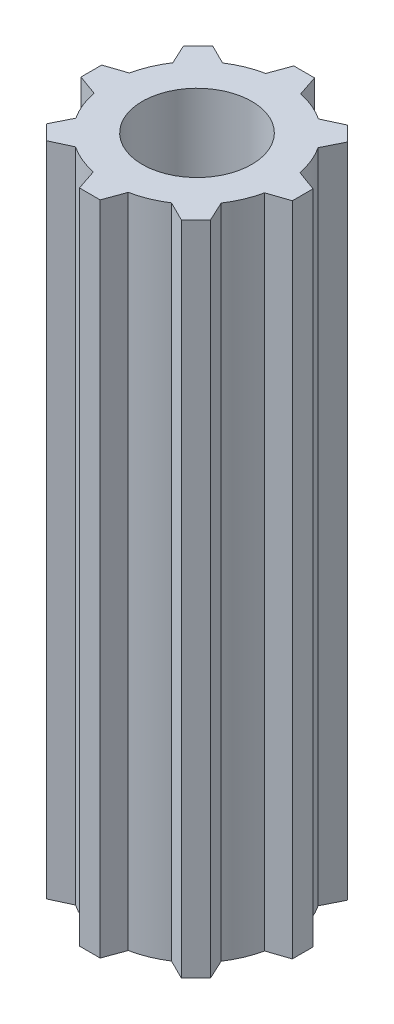
SolidWorks part; units mm, degrees
ref_plane "Front Plane" through (0, 0, 0) normal (0, 0, 1) x (1, 0, 0)
ref_plane "Top Plane" through (0, 0, 0) normal (0, 1, 0) x (1, 0, 0)
ref_plane "Right Plane" through (0, 0, 0) normal (1, 0, 0) x (0, 0, -1)
sketch "Sketch1" plane through (0, 0, 0) normal (0, 1, 0) x (1, 0, 0)
  line L1 (1.0475, 4.9708) -> (0.6449, 6.1753)
  line L2 (4.8226, 3.9106) -> (3.9729, 4.7604)
  line L3 (-0.992, 4.9822) -> (-0.5568, 6.1753)
  line L4 (0.6449, 6.1753) -> (-0.5568, 6.1753)
  line L5 (4.2556, 2.7742) -> (4.8226, 3.9106)
  line L6 (2.8215, 4.2244) -> (3.9729, 4.7604)
  line L7 (6.1753, -0.6449) -> (6.1753, 0.5568)
  line L8 (4.9708, -1.0475) -> (6.1753, -0.6449)
  line L9 (4.9822, 0.992) -> (6.1753, 0.5568)
  line L10 (3.9106, -4.8226) -> (4.7604, -3.9729)
  line L11 (2.7742, -4.2556) -> (3.9106, -4.8226)
  line L12 (4.2244, -2.8215) -> (4.7604, -3.9729)
  line L13 (-0.6449, -6.1753) -> (0.5568, -6.1753)
  line L14 (-1.0475, -4.9708) -> (-0.6449, -6.1753)
  line L15 (0.992, -4.9822) -> (0.5568, -6.1753)
  line L16 (-4.8226, -3.9106) -> (-3.9729, -4.7604)
  line L17 (-4.2556, -2.7742) -> (-4.8226, -3.9106)
  line L18 (-2.8215, -4.2244) -> (-3.9729, -4.7604)
  line L19 (-6.1753, 0.6449) -> (-6.1753, -0.5568)
  line L20 (-4.9708, 1.0475) -> (-6.1753, 0.6449)
  line L21 (-4.9822, -0.992) -> (-6.1753, -0.5568)
  line L22 (-3.9106, 4.8226) -> (-4.7604, 3.9729)
  line L23 (-2.7742, 4.2556) -> (-3.9106, 4.8226)
  line L24 (-4.2244, 2.8215) -> (-4.7604, 3.9729)
  arc A0 (-0.992, 4.9822) -> (-2.7742, 4.2556) centre (0, 0) ccw
  arc A1 (-4.2244, 2.8215) -> (-4.9708, 1.0475) centre (0, 0) ccw
  arc A2 (-4.9822, -0.992) -> (-4.2556, -2.7742) centre (0, 0) ccw
  arc A3 (-2.8215, -4.2244) -> (-1.0475, -4.9708) centre (0, 0) ccw
  arc A4 (0.992, -4.9822) -> (2.7742, -4.2556) centre (0, 0) ccw
  arc A5 (4.2244, -2.8215) -> (4.9708, -1.0475) centre (0, 0) ccw
  arc A6 (4.9822, 0.992) -> (4.2556, 2.7742) centre (0, 0) ccw
  arc A7 (2.8215, 4.2244) -> (1.0475, 4.9708) centre (0, 0) ccw
  point P6 (0, 5.08)
  point P37 (0, 0)
  dimension "D1" = 10.16
  dimension "D2" = 1.27
  dimension "D3" = 1.27
  dimension "D4" = 8
extrude "Boss-Extrude1" add sketch "Sketch1" along normal blind 38.1
sketch "Sketch2" plane through (0, 38.1, 0) normal (0, 1, 0) x (1, 0, 0)
  circle A0 centre (0, 0) radius 3.175
  dimension "D1" = 6.35
extrude "Cut-Extrude1" cut sketch "Sketch2" against normal through all
equation "\"1.8.00in\"=2"
